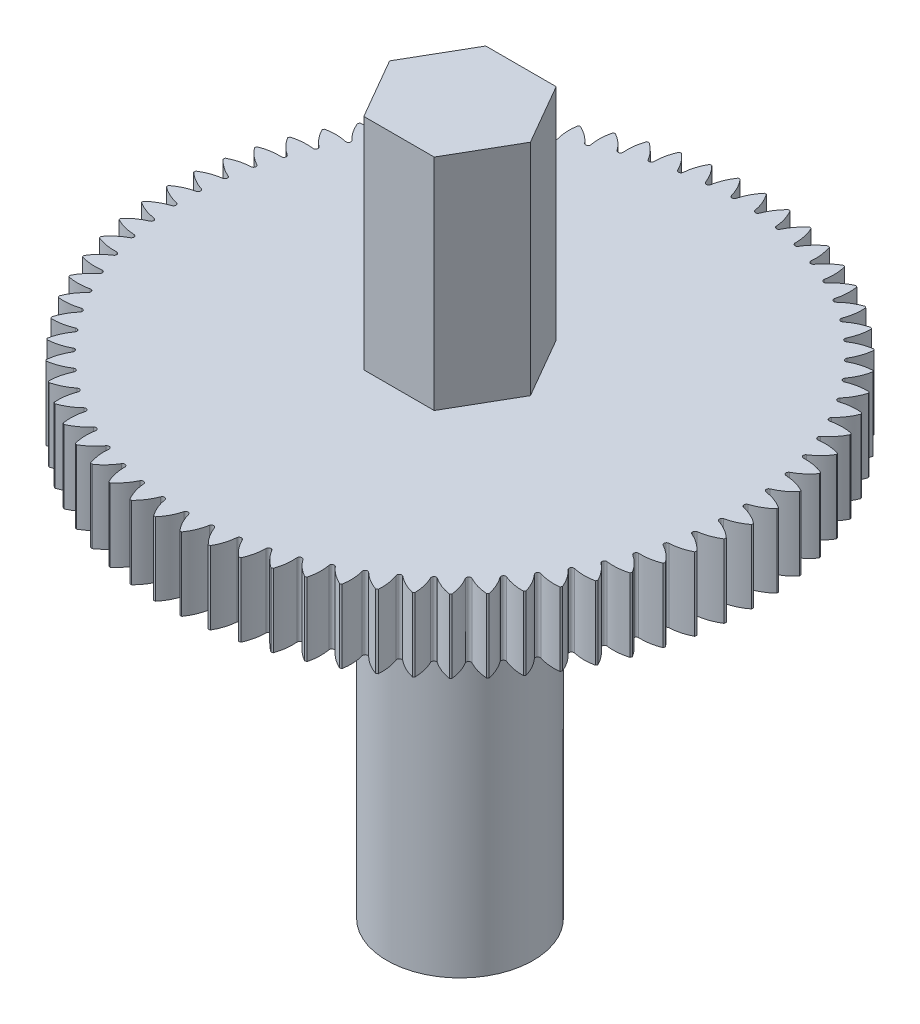
SolidWorks part; units mm, degrees
ref_plane "Front Plane" through (0, 0, 0) normal (0, 0, 1) x (1, 0, 0)
ref_plane "Top Plane" through (0, 0, 0) normal (0, 1, 0) x (1, 0, 0)
ref_plane "Right Plane" through (0, 0, 0) normal (1, 0, 0) x (0, 0, -1)
sketch "Sketch1" plane through (0, 0, 0) normal (0, 0, 1) x (1, 0, 0)
  line L0 (3, 20) -> (3, 29)
  line L1 (0, 0) -> (3, 0)
  line L2 (0, 0) -> (0, 29)
  line L3 (0, 29) -> (3, 29)
  line L4 (3, 0) -> (3, 17)
  line L5 (3, 20) -> (12, 20)
  line L7 (3, 17) -> (12, 17)
  line L8 (12, 20) -> (12, 17)
  dimension "D1" = 3
  dimension "D2" = 29
  dimension "D3" = 3
  dimension "D4" = 9
  dimension "D5" = 17
revolve "Revolve1" add sketch "Sketch1" angle 360 about L2
sketch "Sketch2" plane through (0, 20, 0) normal (0, 1, 0) x (1, 0, 0)
  line L0 (0, 0) -> (0, 12) construction
  circle A0 centre (0, 0) radius 12 construction
  arc A1 (-0.5, 11.9896) -> (0.5, 11.9896) centre (0, 0) cw
  arc A2 (0.5, 11.9896) -> (0.0965, 11.2236) centre (2.0257, 10.6965) ccw
  arc A3 (0.0965, 11.2236) -> (-0.0965, 11.2236) centre (0, 11.25) cw
  arc A4 (-0.5, 11.9896) -> (-0.0965, 11.2236) centre (-2.0257, 10.6965) cw
  dimension "D1" = 1
  dimension "D2" = 2
  dimension "D3" = 0.1
  dimension "D4" = 0.75
extrude "Cut-Extrude1" cut sketch "Sketch2" against normal up to next (3 mm away)
pattern_circular "CirPattern1" count 70 over 360 about axis through (0, 0, 0) along (0, 1, 0) of "Cut-Extrude1"
sketch "Sketch3" plane through (0, 29, 0) normal (0, 1, 0) x (1, 0, 0)
  line L1 (-1.4434, 2.5) -> (-2.8868, 0)
  line L2 (-2.8868, 0) -> (-1.4434, -2.5)
  line L3 (-1.4434, -2.5) -> (1.4434, -2.5)
  line L4 (1.4434, -2.5) -> (2.8868, 0)
  line L5 (2.8868, 0) -> (1.4434, 2.5)
  line L6 (1.4434, 2.5) -> (-1.4434, 2.5)
  circle A0 centre (0, 0) radius 2.5 construction
  circle A1 centre (0, 0) radius 3 construction
  circle A2 centre (0, 0) radius 3
  dimension "D1" = 5
extrude "Cut-Extrude2" cut sketch "Sketch3" against normal up to surface (9 mm away) up to face at (0, 20, 0)
